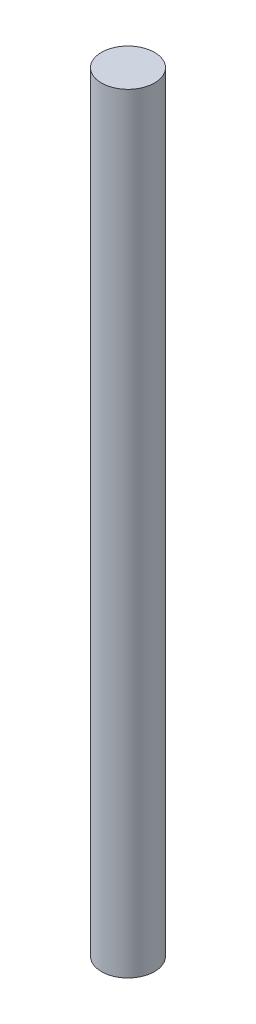
SolidWorks part; units mm, degrees
ref_plane "Front Plane" through (0, 0, 0) normal (0, 0, 1) x (1, 0, 0)
ref_plane "Top Plane" through (0, 0, 0) normal (0, 1, 0) x (1, 0, 0)
ref_plane "Right Plane" through (0, 0, 0) normal (1, 0, 0) x (0, 0, -1)
sketch "Sketch1" plane through (0, 0, 0) normal (0, 1, 0) x (1, 0, 0)
  circle A0 centre (0, 0) radius 1.5
  dimension "D1" = 3
extrude "Boss-Extrude1" add sketch "Sketch1" along normal blind 43.5
